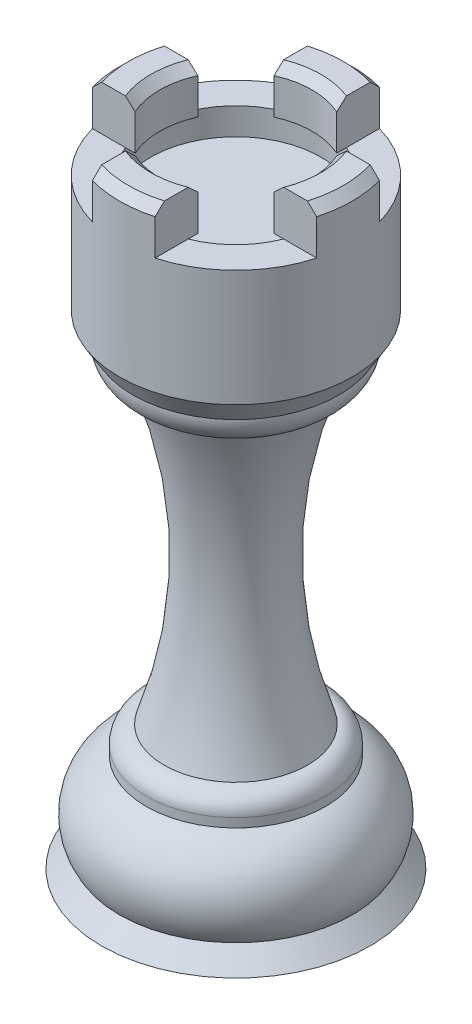
SolidWorks part; units mm, degrees
ref_plane "Front Plane" through (0, 0, 0) normal (0, 0, 1) x (1, 0, 0)
ref_plane "Top Plane" through (0, 0, 0) normal (0, 1, 0) x (1, 0, 0)
ref_plane "Right Plane" through (0, 0, 0) normal (1, 0, 0) x (0, 0, -1)
sketch "Sketch1" plane through (0, 0, 0) normal (0, 0, 1) x (1, 0, 0)
  line L0 (0, 81.0047) -> (0, -25.1351) construction
  line L1 (0, -16.2162) -> (-15, -16.2162)
  line L2 (-15, -16.2162) -> (-15, -13.2162)
  line L3 (-15, -13.2162) -> (0, -13.2162)
  line L5 (-15, -13.2162) -> (-13, -11.2162)
  line L7 (-10, -2.2462) -> (-10, -1.2462)
  line L14 (-11.5, 38.2738) -> (-13, 40.7738)
  line L15 (0, 58.7738) -> (-13, 58.7738)
  line L16 (-13, 40.7738) -> (-13, 58.7738)
  arc A0 (-13, -11.2162) -> (-10, -2.2462) centre (-7.9981, -7.9024) cw
  arc A1 (-10, -1.2462) -> (-8, 0.7538) centre (-8, -1.2462) cw
  arc A2 (-8, 0.7538) -> (-8.5, 34.9538) centre (-55.2293, 17.167) ccw
  arc A3 (-8.5, 34.9538) -> (-11.5, 38.2738) centre (-8.34, 38.1138) cw
  dimension "D6" = 6
  dimension "D13" = 50
  dimension "D1" = 15
  dimension "D2" = 3
  dimension "D8" = 1
  dimension "D19" = 13
revolve "Revolve2" add sketch "Sketch1" angle 360 about L0
sketch "Sketch2" plane through (0, 58.7738, 0) normal (0, 1, 0) x (1, 0, 0)
  line L0 (7.746, 3.5) -> (12.52, 3.5)
  line L1 (3.5, 7.746) -> (3.5, 12.52)
  line L2 (-3.5, 7.746) -> (-3.5, 12.52)
  line L3 (7.746, -3.5) -> (12.52, -3.5)
  line L4 (3.5, -7.746) -> (3.5, -12.52)
  line L5 (-3.5, -7.746) -> (-3.5, -12.52)
  line L6 (-7.746, -3.5) -> (-12.52, -3.5)
  line L7 (-7.746, 3.5) -> (-12.52, 3.5)
  arc A0 (-7.746, -3.5) -> (-3.5, -7.746) centre (0, 0) ccw
  circle A1 centre (0, 0) radius 13
  arc A2 (7.746, 3.5) -> (3.5, 7.746) centre (0, 0) ccw
  arc A3 (-3.5, 7.746) -> (-7.746, 3.5) centre (0, 0) ccw
  arc A4 (3.5, -7.746) -> (7.746, -3.5) centre (0, 0) ccw
  circle M3 centre (0, 0) radius 13
  dimension "D1" = 17
  dimension "D2" = 26
  dimension "D3" = 4
extrude "Cut-Extrude1" cut sketch "Sketch2" against normal blind 5 contours A3 L2 L7 M3 | A0 L6 L5 M3 | A4 L4 L3 M3 | A2 L0 L1 M3
sketch "Sketch3" plane through (0, 58.7738, 0) normal (0, 1, 0) x (1, 0, 0)
  circle A0 centre (0, 0) radius 8.5
  dimension "D1" = 17
extrude "Cut-Extrude2" cut sketch "Sketch3" against normal blind 5
sketch "Sketch5" plane through (0, 53.7738, 0) normal (0, 1, 0) x (1, 0, 0)
  circle A0 centre (0, 0) radius 9.5
  dimension "D1" = 19
extrude "Cut-Extrude3" cut sketch "Sketch5" against normal blind 3
chamfer "Chamfer1" distance 1 angle 45 8 edges at (0, 58.7738, -13) (0, 58.7738, -8.5) (13, 58.7738, 0) (8.5, 58.7738, 0) (0, 58.7738, 13) (0, 58.7738, 8.5) (-13, 58.7738, 0) (-8.5, 58.7738, 0)
